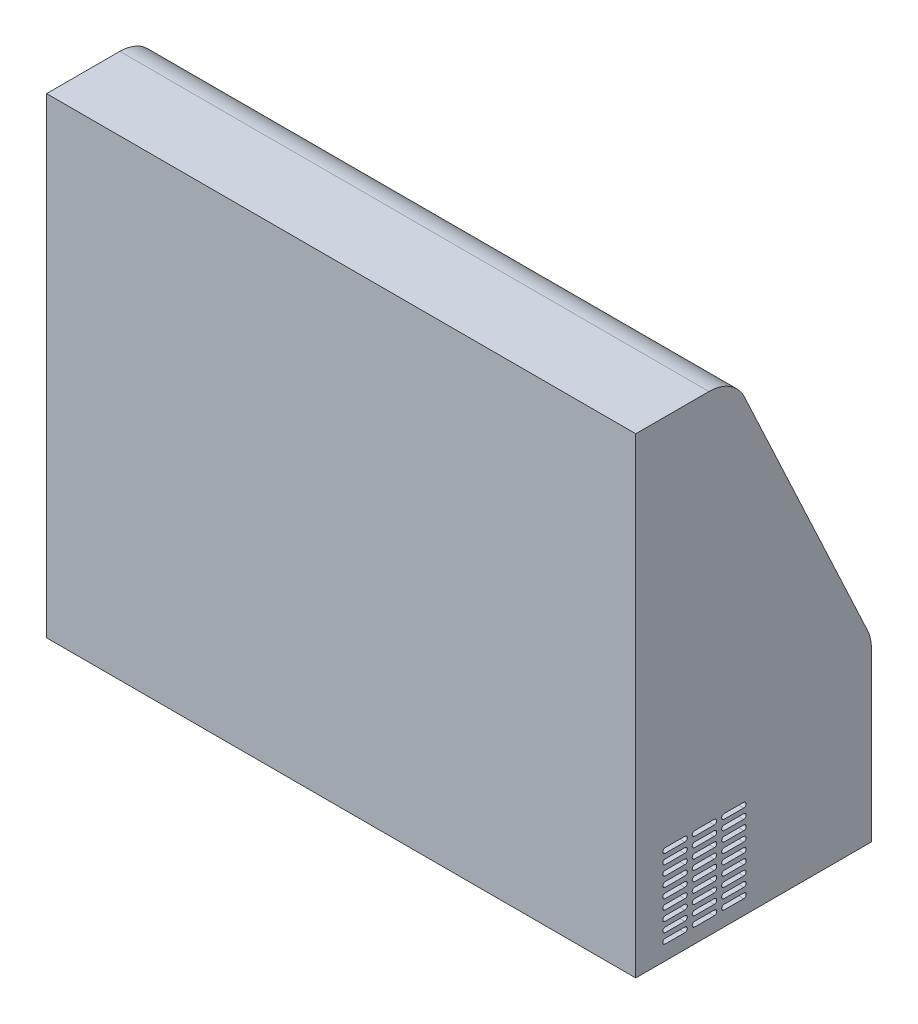
SolidWorks part; units mm, degrees
ref_plane "Front Plane" through (0, 0, 0) normal (0, 0, 1) x (1, 0, 0)
ref_plane "Top Plane" through (0, 0, 0) normal (0, 1, 0) x (1, 0, 0)
ref_plane "Right Plane" through (0, 0, 0) normal (1, 0, 0) x (0, 0, -1)
sketch "Sketch1" plane through (0, 0, 0) normal (0, 0, 1) x (1, 0, 0)
  line L1 (-381, -304.8) -> (381, -304.8)
  line L2 (-381, -304.8) -> (-381, 304.8)
  line L3 (-381, 304.8) -> (381, 304.8)
  line L4 (381, -304.8) -> (381, 304.8)
  line L5 (-381, -304.8) -> (381, 304.8) construction
  line L6 (-381, 304.8) -> (381, -304.8) construction
  point P0 (0, 0)
extrude "Boss-Extrude1" add sketch "Sketch1" along normal blind 304.8
sketch "Sketch6" plane through (0, 0, 0) normal (0, 0, -1) x (-1, 0, 0)
  line L6 (258.064, -136.1872) -> (321.564, -136.1872)
  line L7 (258.064, -136.1872) -> (258.064, -258.4247)
  line L8 (258.064, -258.4247) -> (321.564, -258.4247)
  line L9 (321.564, -136.1872) -> (321.564, -258.4247)
extrude "Cut-Extrude3" cut sketch "Sketch6" against normal blind 12.7
sketch "Sketch7" plane through (381, 0, 0) normal (1, 0, 0) x (0, 0, -1)
  line L3 (-210.1526, 304.8) -> (0, 304.8)
  line L4 (0, -304.8) -> (0, 304.8) construction
  line L5 (-4.7659, -65.9874) -> (-164.1185, 275.4826)
  line L7 (0, 304.8) -> (0, -87.4699)
  arc A0 (-210.1526, 304.8) -> (-164.1185, 275.4826) centre (-210.1526, 254) cw
  arc A1 (0, -87.4699) -> (-4.7659, -65.9874) centre (-50.8, -87.4699) ccw
  point P15 (0, -76.2)
  dimension "D1" = 50.8
  dimension "D2" = 50.8
extrude "Cut-Extrude4" cut sketch "Sketch7" against normal through all
sketch "Sketch8" plane through (0, -13.627, 29.2007) normal (0, 0.4229, -0.9062) x (-1, 0, 0)
  line L6 (-274.701, -40.0581) -> (274.701, -40.0581)
  line L7 (-274.701, -40.0581) -> (-274.701, 301.3179)
  line L8 (-274.701, 301.3179) -> (274.701, 301.3179)
  line L9 (274.701, -40.0581) -> (274.701, 301.3179)
  line L10 (-274.701, -40.0581) -> (274.701, 301.3179) construction
  line L11 (-274.701, 301.3179) -> (274.701, -40.0581) construction
extrude "Cut-Extrude5" cut sketch "Sketch8" against normal blind 50.8
sketch "Sketch11" plane through (381, 0, 0) normal (1, 0, 0) x (0, 0, -1)
  line L0 (-228.6, -177.8) -> (-203.2, -177.8)
  line L1 (-228.6, -184.15) -> (-203.2, -184.15)
  line L6 (-190.5, -177.8) -> (-165.1, -177.8)
  line L7 (-190.5, -184.15) -> (-165.1, -184.15)
  line L8 (-228.6, -190.5) -> (-203.2, -190.5)
  line L9 (-228.6, -196.85) -> (-203.2, -196.85)
  line L10 (-190.5, -190.5) -> (-165.1, -190.5)
  line L11 (-190.5, -196.85) -> (-165.1, -196.85)
  line L12 (-228.6, -203.2) -> (-203.2, -203.2)
  line L13 (-228.6, -209.55) -> (-203.2, -209.55)
  line L14 (-266.7, -177.8) -> (-241.3, -177.8)
  line L15 (-190.5, -203.2) -> (-165.1, -203.2)
  line L16 (-266.7, -184.15) -> (-241.3, -184.15)
  line L17 (-190.5, -209.55) -> (-165.1, -209.55)
  line L18 (-228.6, -215.9) -> (-203.2, -215.9)
  line L19 (-228.6, -222.25) -> (-203.2, -222.25)
  line L20 (-190.5, -215.9) -> (-165.1, -215.9)
  line L21 (-190.5, -222.25) -> (-165.1, -222.25)
  line L22 (-228.6, -228.6) -> (-203.2, -228.6)
  line L23 (-228.6, -234.95) -> (-203.2, -234.95)
  line L24 (-190.5, -228.6) -> (-165.1, -228.6)
  line L25 (-190.5, -234.95) -> (-165.1, -234.95)
  line L26 (-228.6, -241.3) -> (-203.2, -241.3)
  line L27 (-228.6, -247.65) -> (-203.2, -247.65)
  line L28 (-190.5, -241.3) -> (-165.1, -241.3)
  line L29 (-190.5, -247.65) -> (-165.1, -247.65)
  line L30 (-228.6, -254) -> (-203.2, -254)
  line L31 (-228.6, -260.35) -> (-203.2, -260.35)
  line L32 (-190.5, -254) -> (-165.1, -254)
  line L33 (-190.5, -260.35) -> (-165.1, -260.35)
  line L34 (-228.6, -266.7) -> (-203.2, -266.7)
  line L35 (-228.6, -273.05) -> (-203.2, -273.05)
  line L36 (-190.5, -266.7) -> (-165.1, -266.7)
  line L37 (-190.5, -273.05) -> (-165.1, -273.05)
  line L38 (-228.6, -279.4) -> (-203.2, -279.4)
  line L39 (-228.6, -285.75) -> (-203.2, -285.75)
  line L40 (-190.5, -279.4) -> (-165.1, -279.4)
  line L41 (-190.5, -285.75) -> (-165.1, -285.75)
  line L42 (-266.7, -190.5) -> (-241.3, -190.5)
  line L43 (-266.7, -196.85) -> (-241.3, -196.85)
  line L44 (-266.7, -203.2) -> (-241.3, -203.2)
  line L45 (-266.7, -209.55) -> (-241.3, -209.55)
  line L46 (-266.7, -215.9) -> (-241.3, -215.9)
  line L47 (-266.7, -222.25) -> (-241.3, -222.25)
  line L48 (-266.7, -228.6) -> (-241.3, -228.6)
  line L49 (-266.7, -234.95) -> (-241.3, -234.95)
  line L50 (-266.7, -241.3) -> (-241.3, -241.3)
  line L51 (-266.7, -247.65) -> (-241.3, -247.65)
  line L52 (-266.7, -254) -> (-241.3, -254)
  line L53 (-266.7, -260.35) -> (-241.3, -260.35)
  line L54 (-266.7, -266.7) -> (-241.3, -266.7)
  line L55 (-266.7, -273.05) -> (-241.3, -273.05)
  line L56 (-266.7, -279.4) -> (-241.3, -279.4)
  line L57 (-266.7, -285.75) -> (-241.3, -285.75)
  arc A0 (-266.7, -184.15) -> (-266.7, -177.8) centre (-266.7, -180.975) cw
  arc A1 (-241.3, -184.15) -> (-241.3, -177.8) centre (-241.3, -180.975) ccw
  arc A2 (-228.6, -184.15) -> (-228.6, -177.8) centre (-228.6, -180.975) cw
  arc A3 (-203.2, -184.15) -> (-203.2, -177.8) centre (-203.2, -180.975) ccw
  arc A4 (-190.5, -184.15) -> (-190.5, -177.8) centre (-190.5, -180.975) cw
  arc A5 (-165.1, -184.15) -> (-165.1, -177.8) centre (-165.1, -180.975) ccw
  arc A6 (-228.6, -196.85) -> (-228.6, -190.5) centre (-228.6, -193.675) cw
  arc A7 (-203.2, -196.85) -> (-203.2, -190.5) centre (-203.2, -193.675) ccw
  arc A8 (-190.5, -196.85) -> (-190.5, -190.5) centre (-190.5, -193.675) cw
  arc A9 (-165.1, -196.85) -> (-165.1, -190.5) centre (-165.1, -193.675) ccw
  arc A10 (-228.6, -209.55) -> (-228.6, -203.2) centre (-228.6, -206.375) cw
  arc A11 (-203.2, -209.55) -> (-203.2, -203.2) centre (-203.2, -206.375) ccw
  arc A12 (-190.5, -209.55) -> (-190.5, -203.2) centre (-190.5, -206.375) cw
  arc A13 (-165.1, -209.55) -> (-165.1, -203.2) centre (-165.1, -206.375) ccw
  arc A14 (-228.6, -222.25) -> (-228.6, -215.9) centre (-228.6, -219.075) cw
  arc A15 (-203.2, -222.25) -> (-203.2, -215.9) centre (-203.2, -219.075) ccw
  arc A16 (-190.5, -222.25) -> (-190.5, -215.9) centre (-190.5, -219.075) cw
  arc A17 (-165.1, -222.25) -> (-165.1, -215.9) centre (-165.1, -219.075) ccw
  arc A18 (-228.6, -234.95) -> (-228.6, -228.6) centre (-228.6, -231.775) cw
  arc A19 (-203.2, -234.95) -> (-203.2, -228.6) centre (-203.2, -231.775) ccw
  arc A20 (-190.5, -234.95) -> (-190.5, -228.6) centre (-190.5, -231.775) cw
  arc A21 (-165.1, -234.95) -> (-165.1, -228.6) centre (-165.1, -231.775) ccw
  arc A22 (-228.6, -247.65) -> (-228.6, -241.3) centre (-228.6, -244.475) cw
  arc A23 (-203.2, -247.65) -> (-203.2, -241.3) centre (-203.2, -244.475) ccw
  arc A24 (-190.5, -247.65) -> (-190.5, -241.3) centre (-190.5, -244.475) cw
  arc A25 (-165.1, -247.65) -> (-165.1, -241.3) centre (-165.1, -244.475) ccw
  arc A26 (-228.6, -260.35) -> (-228.6, -254) centre (-228.6, -257.175) cw
  arc A27 (-203.2, -260.35) -> (-203.2, -254) centre (-203.2, -257.175) ccw
  arc A28 (-190.5, -260.35) -> (-190.5, -254) centre (-190.5, -257.175) cw
  arc A29 (-165.1, -260.35) -> (-165.1, -254) centre (-165.1, -257.175) ccw
  arc A30 (-228.6, -273.05) -> (-228.6, -266.7) centre (-228.6, -269.875) cw
  arc A31 (-203.2, -273.05) -> (-203.2, -266.7) centre (-203.2, -269.875) ccw
  arc A32 (-190.5, -273.05) -> (-190.5, -266.7) centre (-190.5, -269.875) cw
  arc A33 (-165.1, -273.05) -> (-165.1, -266.7) centre (-165.1, -269.875) ccw
  arc A34 (-228.6, -285.75) -> (-228.6, -279.4) centre (-228.6, -282.575) cw
  arc A35 (-203.2, -285.75) -> (-203.2, -279.4) centre (-203.2, -282.575) ccw
  arc A36 (-190.5, -285.75) -> (-190.5, -279.4) centre (-190.5, -282.575) cw
  arc A37 (-165.1, -285.75) -> (-165.1, -279.4) centre (-165.1, -282.575) ccw
  arc A38 (-266.7, -196.85) -> (-266.7, -190.5) centre (-266.7, -193.675) cw
  arc A39 (-241.3, -196.85) -> (-241.3, -190.5) centre (-241.3, -193.675) ccw
  arc A40 (-266.7, -209.55) -> (-266.7, -203.2) centre (-266.7, -206.375) cw
  arc A41 (-241.3, -209.55) -> (-241.3, -203.2) centre (-241.3, -206.375) ccw
  arc A42 (-266.7, -222.25) -> (-266.7, -215.9) centre (-266.7, -219.075) cw
  arc A43 (-241.3, -222.25) -> (-241.3, -215.9) centre (-241.3, -219.075) ccw
  arc A44 (-266.7, -234.95) -> (-266.7, -228.6) centre (-266.7, -231.775) cw
  arc A45 (-241.3, -234.95) -> (-241.3, -228.6) centre (-241.3, -231.775) ccw
  arc A46 (-266.7, -247.65) -> (-266.7, -241.3) centre (-266.7, -244.475) cw
  arc A47 (-241.3, -247.65) -> (-241.3, -241.3) centre (-241.3, -244.475) ccw
  arc A48 (-266.7, -260.35) -> (-266.7, -254) centre (-266.7, -257.175) cw
  arc A49 (-241.3, -260.35) -> (-241.3, -254) centre (-241.3, -257.175) ccw
  arc A50 (-266.7, -273.05) -> (-266.7, -266.7) centre (-266.7, -269.875) cw
  arc A51 (-241.3, -273.05) -> (-241.3, -266.7) centre (-241.3, -269.875) ccw
  arc A52 (-266.7, -285.75) -> (-266.7, -279.4) centre (-266.7, -282.575) cw
  arc A53 (-241.3, -285.75) -> (-241.3, -279.4) centre (-241.3, -282.575) ccw
  dimension "D1" = 3
  dimension "D2" = 9
extrude "Cut-Extrude6" cut sketch "Sketch11" against normal blind 50.8
sketch "Sketch12" plane through (0, -304.8, 0) normal (0, -1, 0) x (1, 0, 0)
  line L0 (-289.0185, 250.9185) -> (-263.6185, 250.9185)
  line L1 (-289.0185, 244.5685) -> (-263.6185, 244.5685)
  line L2 (-250.9185, 250.9185) -> (-225.5185, 250.9185)
  line L3 (-250.9185, 244.5685) -> (-225.5185, 244.5685)
  line L4 (-289.0185, 238.2185) -> (-263.6185, 238.2185)
  line L5 (-289.0185, 231.8685) -> (-263.6185, 231.8685)
  line L6 (-250.9185, 238.2185) -> (-225.5185, 238.2185)
  line L7 (-250.9185, 231.8685) -> (-225.5185, 231.8685)
  line L8 (-289.0185, 225.5185) -> (-263.6185, 225.5185)
  line L9 (-289.0185, 219.1685) -> (-263.6185, 219.1685)
  line L10 (-327.1185, 250.9185) -> (-301.7185, 250.9185)
  line L11 (-250.9185, 225.5185) -> (-225.5185, 225.5185)
  line L12 (-327.1185, 244.5685) -> (-301.7185, 244.5685)
  line L13 (-250.9185, 219.1685) -> (-225.5185, 219.1685)
  line L14 (-289.0185, 212.8185) -> (-263.6185, 212.8185)
  line L15 (-289.0185, 206.4685) -> (-263.6185, 206.4685)
  line L16 (-250.9185, 212.8185) -> (-225.5185, 212.8185)
  line L17 (-250.9185, 206.4685) -> (-225.5185, 206.4685)
  line L18 (-289.0185, 200.1185) -> (-263.6185, 200.1185)
  line L19 (-289.0185, 193.7685) -> (-263.6185, 193.7685)
  line L20 (-250.9185, 200.1185) -> (-225.5185, 200.1185)
  line L21 (-250.9185, 193.7685) -> (-225.5185, 193.7685)
  line L22 (-289.0185, 187.4185) -> (-263.6185, 187.4185)
  line L23 (-289.0185, 181.0685) -> (-263.6185, 181.0685)
  line L24 (-250.9185, 187.4185) -> (-225.5185, 187.4185)
  line L25 (-250.9185, 181.0685) -> (-225.5185, 181.0685)
  line L26 (-289.0185, 174.7185) -> (-263.6185, 174.7185)
  line L27 (-289.0185, 168.3685) -> (-263.6185, 168.3685)
  line L28 (-250.9185, 174.7185) -> (-225.5185, 174.7185)
  line L29 (-250.9185, 168.3685) -> (-225.5185, 168.3685)
  line L30 (-289.0185, 162.0185) -> (-263.6185, 162.0185)
  line L31 (-289.0185, 155.6685) -> (-263.6185, 155.6685)
  line L32 (-250.9185, 162.0185) -> (-225.5185, 162.0185)
  line L33 (-250.9185, 155.6685) -> (-225.5185, 155.6685)
  line L34 (-289.0185, 149.3185) -> (-263.6185, 149.3185)
  line L35 (-289.0185, 142.9685) -> (-263.6185, 142.9685)
  line L36 (-250.9185, 149.3185) -> (-225.5185, 149.3185)
  line L37 (-250.9185, 142.9685) -> (-225.5185, 142.9685)
  line L38 (-327.1185, 238.2185) -> (-301.7185, 238.2185)
  line L39 (-327.1185, 231.8685) -> (-301.7185, 231.8685)
  line L40 (-327.1185, 225.5185) -> (-301.7185, 225.5185)
  line L41 (-327.1185, 219.1685) -> (-301.7185, 219.1685)
  line L42 (-327.1185, 212.8185) -> (-301.7185, 212.8185)
  line L43 (-327.1185, 206.4685) -> (-301.7185, 206.4685)
  line L44 (-327.1185, 200.1185) -> (-301.7185, 200.1185)
  line L45 (-327.1185, 193.7685) -> (-301.7185, 193.7685)
  line L46 (-327.1185, 187.4185) -> (-301.7185, 187.4185)
  line L47 (-327.1185, 181.0685) -> (-301.7185, 181.0685)
  line L48 (-327.1185, 174.7185) -> (-301.7185, 174.7185)
  line L49 (-327.1185, 168.3685) -> (-301.7185, 168.3685)
  line L50 (-327.1185, 162.0185) -> (-301.7185, 162.0185)
  line L51 (-327.1185, 155.6685) -> (-301.7185, 155.6685)
  line L52 (-327.1185, 149.3185) -> (-301.7185, 149.3185)
  line L53 (-327.1185, 142.9685) -> (-301.7185, 142.9685)
  arc A0 (-327.1185, 244.5685) -> (-327.1185, 250.9185) centre (-327.1185, 247.7435) cw
  arc A1 (-301.7185, 244.5685) -> (-301.7185, 250.9185) centre (-301.7185, 247.7435) ccw
  arc A2 (-289.0185, 244.5685) -> (-289.0185, 250.9185) centre (-289.0185, 247.7435) cw
  arc A3 (-263.6185, 244.5685) -> (-263.6185, 250.9185) centre (-263.6185, 247.7435) ccw
  arc A4 (-250.9185, 244.5685) -> (-250.9185, 250.9185) centre (-250.9185, 247.7435) cw
  arc A5 (-225.5185, 244.5685) -> (-225.5185, 250.9185) centre (-225.5185, 247.7435) ccw
  arc A6 (-289.0185, 231.8685) -> (-289.0185, 238.2185) centre (-289.0185, 235.0435) cw
  arc A7 (-263.6185, 231.8685) -> (-263.6185, 238.2185) centre (-263.6185, 235.0435) ccw
  arc A8 (-250.9185, 231.8685) -> (-250.9185, 238.2185) centre (-250.9185, 235.0435) cw
  arc A9 (-225.5185, 231.8685) -> (-225.5185, 238.2185) centre (-225.5185, 235.0435) ccw
  arc A10 (-289.0185, 219.1685) -> (-289.0185, 225.5185) centre (-289.0185, 222.3435) cw
  arc A11 (-263.6185, 219.1685) -> (-263.6185, 225.5185) centre (-263.6185, 222.3435) ccw
  arc A12 (-250.9185, 219.1685) -> (-250.9185, 225.5185) centre (-250.9185, 222.3435) cw
  arc A13 (-225.5185, 219.1685) -> (-225.5185, 225.5185) centre (-225.5185, 222.3435) ccw
  arc A14 (-289.0185, 206.4685) -> (-289.0185, 212.8185) centre (-289.0185, 209.6435) cw
  arc A15 (-263.6185, 206.4685) -> (-263.6185, 212.8185) centre (-263.6185, 209.6435) ccw
  arc A16 (-250.9185, 206.4685) -> (-250.9185, 212.8185) centre (-250.9185, 209.6435) cw
  arc A17 (-225.5185, 206.4685) -> (-225.5185, 212.8185) centre (-225.5185, 209.6435) ccw
  arc A18 (-289.0185, 193.7685) -> (-289.0185, 200.1185) centre (-289.0185, 196.9435) cw
  arc A19 (-263.6185, 193.7685) -> (-263.6185, 200.1185) centre (-263.6185, 196.9435) ccw
  arc A20 (-250.9185, 193.7685) -> (-250.9185, 200.1185) centre (-250.9185, 196.9435) cw
  arc A21 (-225.5185, 193.7685) -> (-225.5185, 200.1185) centre (-225.5185, 196.9435) ccw
  arc A22 (-289.0185, 181.0685) -> (-289.0185, 187.4185) centre (-289.0185, 184.2435) cw
  arc A23 (-263.6185, 181.0685) -> (-263.6185, 187.4185) centre (-263.6185, 184.2435) ccw
  arc A24 (-250.9185, 181.0685) -> (-250.9185, 187.4185) centre (-250.9185, 184.2435) cw
  arc A25 (-225.5185, 181.0685) -> (-225.5185, 187.4185) centre (-225.5185, 184.2435) ccw
  arc A26 (-289.0185, 168.3685) -> (-289.0185, 174.7185) centre (-289.0185, 171.5435) cw
  arc A27 (-263.6185, 168.3685) -> (-263.6185, 174.7185) centre (-263.6185, 171.5435) ccw
  arc A28 (-250.9185, 168.3685) -> (-250.9185, 174.7185) centre (-250.9185, 171.5435) cw
  arc A29 (-225.5185, 168.3685) -> (-225.5185, 174.7185) centre (-225.5185, 171.5435) ccw
  arc A30 (-289.0185, 155.6685) -> (-289.0185, 162.0185) centre (-289.0185, 158.8435) cw
  arc A31 (-263.6185, 155.6685) -> (-263.6185, 162.0185) centre (-263.6185, 158.8435) ccw
  arc A32 (-250.9185, 155.6685) -> (-250.9185, 162.0185) centre (-250.9185, 158.8435) cw
  arc A33 (-225.5185, 155.6685) -> (-225.5185, 162.0185) centre (-225.5185, 158.8435) ccw
  arc A34 (-289.0185, 142.9685) -> (-289.0185, 149.3185) centre (-289.0185, 146.1435) cw
  arc A35 (-263.6185, 142.9685) -> (-263.6185, 149.3185) centre (-263.6185, 146.1435) ccw
  arc A36 (-250.9185, 142.9685) -> (-250.9185, 149.3185) centre (-250.9185, 146.1435) cw
  arc A37 (-225.5185, 142.9685) -> (-225.5185, 149.3185) centre (-225.5185, 146.1435) ccw
  arc A38 (-327.1185, 231.8685) -> (-327.1185, 238.2185) centre (-327.1185, 235.0435) cw
  arc A39 (-301.7185, 231.8685) -> (-301.7185, 238.2185) centre (-301.7185, 235.0435) ccw
  arc A40 (-327.1185, 219.1685) -> (-327.1185, 225.5185) centre (-327.1185, 222.3435) cw
  arc A41 (-301.7185, 219.1685) -> (-301.7185, 225.5185) centre (-301.7185, 222.3435) ccw
  arc A42 (-327.1185, 206.4685) -> (-327.1185, 212.8185) centre (-327.1185, 209.6435) cw
  arc A43 (-301.7185, 206.4685) -> (-301.7185, 212.8185) centre (-301.7185, 209.6435) ccw
  arc A44 (-327.1185, 193.7685) -> (-327.1185, 200.1185) centre (-327.1185, 196.9435) cw
  arc A45 (-301.7185, 193.7685) -> (-301.7185, 200.1185) centre (-301.7185, 196.9435) ccw
  arc A46 (-327.1185, 181.0685) -> (-327.1185, 187.4185) centre (-327.1185, 184.2435) cw
  arc A47 (-301.7185, 181.0685) -> (-301.7185, 187.4185) centre (-301.7185, 184.2435) ccw
  arc A48 (-327.1185, 168.3685) -> (-327.1185, 174.7185) centre (-327.1185, 171.5435) cw
  arc A49 (-301.7185, 168.3685) -> (-301.7185, 174.7185) centre (-301.7185, 171.5435) ccw
  arc A50 (-327.1185, 155.6685) -> (-327.1185, 162.0185) centre (-327.1185, 158.8435) cw
  arc A51 (-301.7185, 155.6685) -> (-301.7185, 162.0185) centre (-301.7185, 158.8435) ccw
  arc A52 (-327.1185, 142.9685) -> (-327.1185, 149.3185) centre (-327.1185, 146.1435) cw
  arc A53 (-301.7185, 142.9685) -> (-301.7185, 149.3185) centre (-301.7185, 146.1435) ccw
extrude "Cut-Extrude7" cut sketch "Sketch12" against normal blind 50.8
sketch "Sketch15" plane through (0, 0, 0) normal (1, 0, 0) x (0, 0, -1)
  line L8 (-62.3085, -92.8406) -> (-221.6612, 248.6294)
  line L9 (-221.6612, 248.6294) -> (-175.6271, 270.1119)
  line L10 (-62.3085, -92.8406) -> (-16.2744, -71.358)
  line L12 (-210.1526, 292.1) -> (-292.1, 292.1)
  line L13 (-16.2744, -71.358) -> (-175.6271, 270.1119)
  line L14 (-12.7, -292.1) -> (-12.7, -87.4699)
  line L15 (-292.1, -292.1) -> (-12.7, -292.1)
  line L16 (-292.1, 292.1) -> (-292.1, -292.1)
  line L17 (-210.1526, 292.1) -> (-292.1, 292.1)
  line L19 (-12.7, -292.1) -> (-12.7, -87.4699)
  line L20 (-292.1, -292.1) -> (-12.7, -292.1)
  line L21 (-292.1, 292.1) -> (-292.1, -292.1)
  arc A5 (-175.6271, 270.1119) -> (-210.1526, 292.1) centre (-210.1526, 254) ccw
  arc A6 (-12.7, -87.4699) -> (-16.2744, -71.358) centre (-50.8, -87.4699) ccw
  arc A7 (-175.6271, 270.1119) -> (-210.1526, 292.1) centre (-210.1526, 254) ccw
  arc A8 (-12.7, -87.4699) -> (-16.2744, -71.358) centre (-50.8, -87.4699) ccw
  dimension "D1" = 12.7
extrude "Cut-Extrude9" cut sketch "Sketch15" against normal blind 368.3 and the other way blind 368.3
